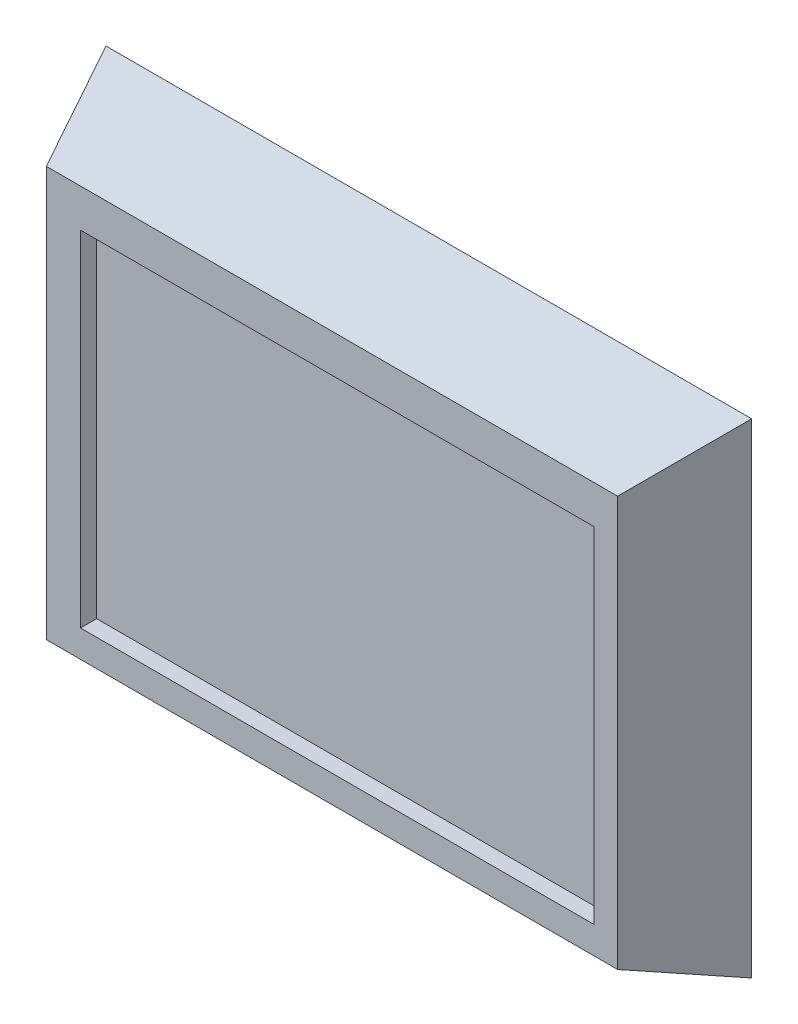
SolidWorks part; units mm, degrees
ref_plane "Ön Düzlem" through (0, 0, 0) normal (0, 0, 1) x (1, 0, 0)
ref_plane "Üst Düzlem" through (0, 0, 0) normal (0, 1, 0) x (1, 0, 0)
ref_plane "Sağ Düzlem" through (0, 0, 0) normal (1, 0, 0) x (0, 0, -1)
sketch "Çizim1" plane through (0, 0, 0) normal (0, 0, 1) x (1, 0, 0)
  line L1 (0, 0) -> (200, 0)
  line L2 (0, 0) -> (0, 150)
  line L3 (0, 150) -> (200, 150)
  line L4 (200, 0) -> (200, 150)
  dimension "D1" = 200
  dimension "D2" = 150
extrude "Yükseklik-Ekstrüzyon1" add sketch "Çizim1" along normal blind 30 draft 21
sketch "Çizim2" plane through (0, 0, 30) normal (0, 0, 1) x (1, 0, 0)
  line L1 (22.1027, 126.6629) -> (181.2052, 126.6629)
  line L2 (22.1027, 126.6629) -> (22.1027, 19.9401)
  line L3 (22.1027, 19.9401) -> (181.2052, 19.9401)
  line L4 (181.2052, 126.6629) -> (181.2052, 19.9401)
extrude "Kes-Ekstrüzyon1" cut sketch "Çizim2" against normal blind 5
